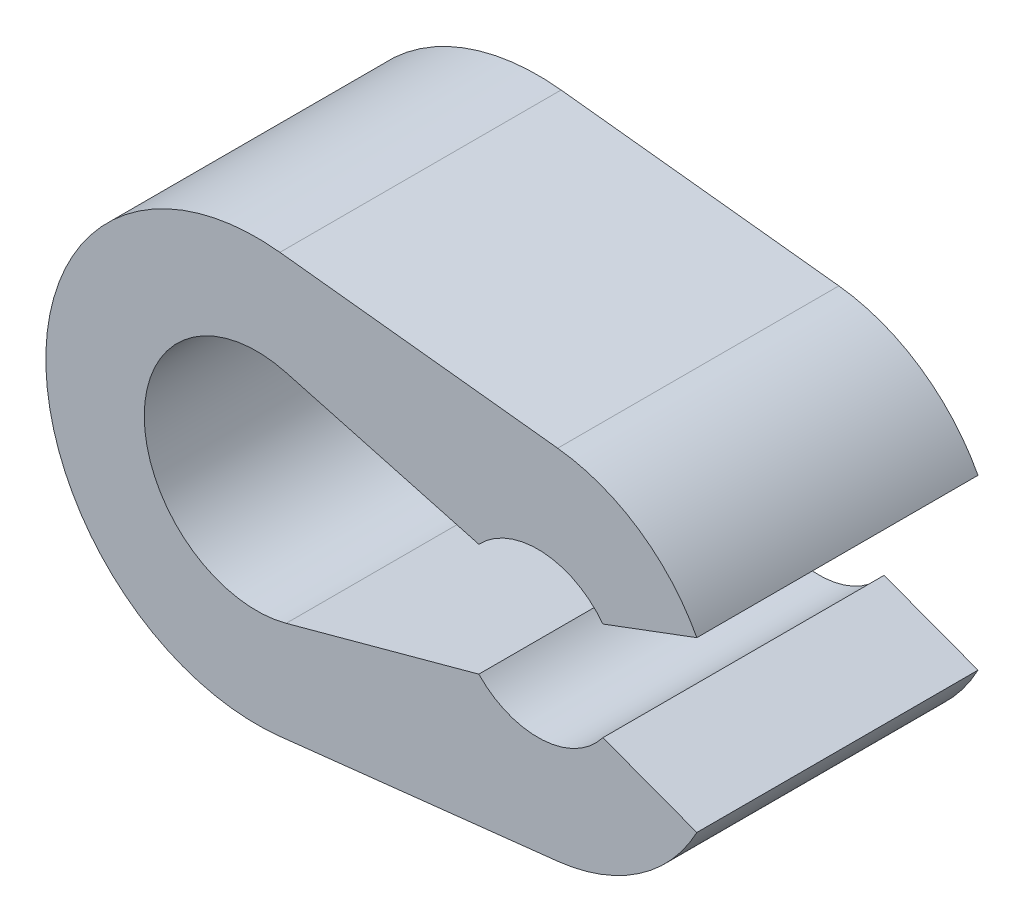
SolidWorks part; units mm, degrees
ref_plane "Plan de face" through (0, 0, 0) normal (0, 0, 1) x (1, 0, 0)
ref_plane "Plan de dessus" through (0, 0, 0) normal (0, 1, 0) x (1, 0, 0)
ref_plane "Plan de droite" through (0, 0, 0) normal (1, 0, 0) x (0, 0, -1)
sketch "Esquisse1" plane through (0, 0, 0) normal (0, 0, 1) x (1, 0, 0)
  line L0 (-9.175, 7.4545) -> (0.704, 6.3612)
  line L1 (-9.175, -7.4545) -> (0.704, -6.3612)
  line L2 (2.3125, 1.75) -> (5.6533, 3)
  line L3 (2.3125, -1.75) -> (5.6533, -3)
  line L4 (-8.952, 3.8603) -> (-2.1, 2)
  line L5 (-8.952, -3.8603) -> (-2.1, -2)
  arc A0 (-2.1, -2) -> (2.3125, -1.75) centre (0, 0) ccw
  arc A1 (-8.952, 3.8603) -> (-8.952, -3.8603) centre (-10, 0) ccw
  arc A2 (-8.7395, 7.3933) -> (-9.175, -7.4545) centre (-10, 0) ccw
  arc A3 (0.704, -6.3612) -> (5.6533, -3) centre (0, 0) ccw
  circle A4 centre (-10, 0) radius 4 construction
  circle A5 centre (0, 0) radius 6.4 construction
  circle A6 centre (-10, 0) radius 7.5 construction
  circle A7 centre (0, 0) radius 2.9 construction
  arc A8 (2.3125, 1.75) -> (-2.1, 2) centre (0, 0) ccw
  arc A9 (5.6533, 3) -> (0.704, 6.3612) centre (0, 0) ccw
  dimension "D1" = 5.8
  dimension "D2" = 8
  dimension "D3" = 10
  dimension "D5" = 3.5
  dimension "D6" = 6
  dimension "D7" = 4
  dimension "D4" = 3.5
extrude "Boss.-Extru.1" add sketch "Esquisse1" along normal blind 10 contours L2 A9 A2 A3 L3 A0 L5 A1 L4 A8
